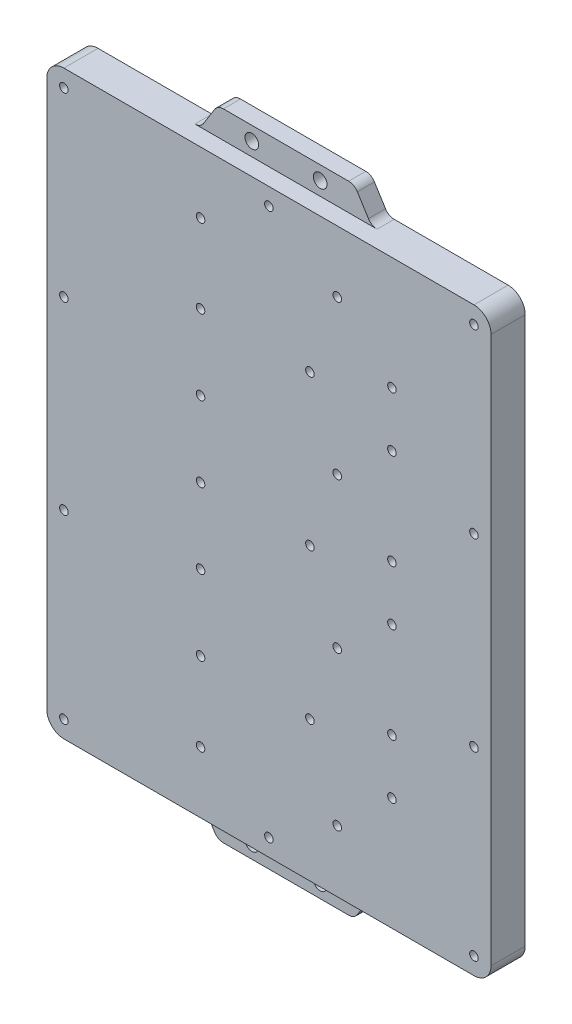
SolidWorks part; units mm, degrees
ref_plane "Front Plane" through (0, 0, 0) normal (0, 0, 1) x (1, 0, 0)
ref_plane "Top Plane" through (0, 0, 0) normal (0, 1, 0) x (1, 0, 0)
ref_plane "Right Plane" through (0, 0, 0) normal (1, 0, 0) x (0, 0, -1)
sketch "Sketch1" plane through (0, 0, 0) normal (0, 0, 1) x (1, 0, 0)
  line L0 (0, 0) -> (0, 173.9814) construction
  line L1 (-60, -85) -> (-26.6627, -85)
  line L2 (-65, -80) -> (-65, 80)
  line L3 (-60, 85) -> (-26.6627, 85)
  line L4 (65, -80) -> (65, 80)
  line L5 (-65, -85) -> (65, 85) construction
  line L6 (-65, 85) -> (65, -85) construction
  line L7 (18.3373, 93) -> (-18.3373, 93)
  line L8 (20.8813, 91.59) -> (24.1187, 86.41)
  line L9 (26.6627, 85) -> (60, 85)
  line L10 (-20.8813, 91.59) -> (-24.1187, 86.41)
  line L11 (0, 0) -> (119.7627, 0) construction
  line L12 (20.8813, -91.59) -> (24.1187, -86.41)
  line L13 (18.3373, -93) -> (-18.3373, -93)
  line L14 (-20.8813, -91.59) -> (-24.1187, -86.41)
  line L15 (26.6627, -85) -> (60, -85)
  arc A0 (-60, -85) -> (-65, -80) centre (-60, -80) cw
  arc A1 (60, -85) -> (65, -80) centre (60, -80) ccw
  arc A2 (60, 85) -> (65, 80) centre (60, 80) cw
  arc A3 (-65, 80) -> (-60, 85) centre (-60, 80) cw
  arc A4 (18.3373, 93) -> (20.8813, 91.59) centre (18.3373, 90) cw
  arc A5 (24.1187, 86.41) -> (26.6627, 85) centre (26.6627, 88) ccw
  arc A6 (-24.1187, 86.41) -> (-26.6627, 85) centre (-26.6627, 88) cw
  arc A7 (-18.3373, 93) -> (-20.8813, 91.59) centre (-18.3373, 90) ccw
  arc A8 (24.1187, -86.41) -> (26.6627, -85) centre (26.6627, -88) cw
  arc A9 (18.3373, -93) -> (20.8813, -91.59) centre (18.3373, -90) ccw
  arc A10 (-18.3373, -93) -> (-20.8813, -91.59) centre (-18.3373, -90) cw
  arc A11 (-24.1187, -86.41) -> (-26.6627, -85) centre (-26.6627, -88) ccw
  circle A12 centre (-10, 89) radius 2
  circle A13 centre (10, 89) radius 2
  circle A14 centre (10, -89) radius 2
  circle A15 centre (-10, -89) radius 2
  point P0 (0, 0)
  point P26 (20, 93)
  point P30 (25, 85)
  point P37 (0, 93)
  point P52 (-8.8094, 89.1796)
  point P53 (-7.2007, 90.1588)
  dimension "D3" = 5
  dimension "D7" = 3
  dimension "D8" = 3
  dimension "D11" = 4
  dimension "D1" = 130
  dimension "D2" = 170
  dimension "D4" = 8
  dimension "D5" = 20
  dimension "D6" = 25
  dimension "D9" = 10
  dimension "D10" = 4
extrude "Boss-Extrude1" add sketch "Sketch1" along normal blind 5
sketch "Sketch2" plane through (0, 0, 5) normal (0, 0, 1) x (1, 0, 0)
  line L1 (60, -85) -> (-60, -85)
  line L2 (65, -80) -> (65, 80)
  line L3 (60, 85) -> (-60, 85)
  line L4 (-65, -80) -> (-65, 80)
  line L5 (65, -85) -> (-65, 85) construction
  line L6 (65, 85) -> (-65, -85) construction
  arc A0 (-65, 80) -> (-60, 85) centre (-60, 80) cw
  arc A1 (60, 85) -> (65, 80) centre (60, 80) cw
  arc A2 (65, -80) -> (60, -85) centre (60, -80) cw
  arc A3 (-60, -85) -> (-65, -80) centre (-60, -80) cw
  arc A4 (-65, -80) -> (-60, -85) centre (-60, -80) ccw construction
  point P0 (0, 0)
extrude "Boss-Extrude2" add sketch "Sketch2" along normal blind 5
sketch "Sketch3" plane through (0, 0, 10) normal (0, 0, 1) x (1, 0, 0)
  line L0 (0, 0) -> (0, 112.7177) construction
  line L1 (0, 0) -> (126.367, 0) construction
  line L2 (-20, 106.3032) -> (-20, -110.6955) construction
  line L3 (36, 108.5453) -> (36, -108.1132) construction
  line L4 (-65, 80) -> (-65, -80) construction
  line L5 (-60, -85) -> (60, -85) construction
  line L7 (-20, -67) -> (21.9568, -67) construction
  line L8 (-20, -44) -> (26.4429, -44) construction
  circle A0 centre (60, -27) radius 1.25
  circle A1 centre (60, -80) radius 1.25
  circle A2 centre (-60, -27) radius 1.25
  circle A3 centre (-60, -80) radius 1.25
  circle A4 centre (0, -80) radius 1.25
  circle A5 centre (60, 27) radius 1.25
  circle A6 centre (60, 80) radius 1.25
  circle A7 centre (0, 80) radius 1.25
  circle A8 centre (-60, 27) radius 1.25
  circle A9 centre (-60, 80) radius 1.25
  circle A10 centre (-20, -67) radius 1.25
  circle A11 centre (-20, -44) radius 1.25
  circle A12 centre (-20, -22) radius 1.25
  circle A13 centre (-20, 0) radius 1.25
  circle A14 centre (-20, 22) radius 1.25
  circle A15 centre (-20, 44) radius 1.25
  circle A16 centre (-20, 67) radius 1.25
  circle A17 centre (36, -52) radius 1.25
  circle A18 centre (36, -36) radius 1.25
  circle A19 centre (36, 8) radius 1.25
  circle A20 centre (36, -8) radius 1.25
  circle A21 centre (36, 52) radius 1.25
  circle A22 centre (36, 36) radius 1.25
  circle A23 centre (20, -67) radius 1.25
  circle A24 centre (20, -22) radius 1.25
  circle A25 centre (20, 22) radius 1.25
  circle A26 centre (20, 67) radius 1.25
  circle A27 centre (12, -44) radius 1.25
  circle A28 centre (12, 0) radius 1.25
  circle A29 centre (12, 44) radius 1.25
  dimension "D2" = 2.5
  dimension "D3" = 2.5
  dimension "D4" = 2.5
  dimension "D7" = 2.5
  dimension "D8" = 2.5
  dimension "D13" = 2.5
  dimension "D15" = 2
  dimension "D16" = 2.5
  dimension "D20" = 2.5
  dimension "D1" = 27
  dimension "D5" = 45
  dimension "D6" = 101
  dimension "D9" = 18
  dimension "D10" = 23
  dimension "D14" = 33
  dimension "D17" = 40
  dimension "D21" = 32
  dimension "D11" = 5
  dimension "D12" = 2
  dimension "D18" = 2
  dimension "D19" = 2
extrude "Cut-Extrude1" cut sketch "Sketch3" against normal blind 5
cosmetic thread "Cosmetic Thread1"
cosmetic thread "Cosmetic Thread2"
cosmetic thread "Cosmetic Thread3"
cosmetic thread "Cosmetic Thread4"
cosmetic thread "Cosmetic Thread5"
cosmetic thread "Cosmetic Thread6"
cosmetic thread "Cosmetic Thread7"
cosmetic thread "Cosmetic Thread8"
cosmetic thread "Cosmetic Thread9"
cosmetic thread "Cosmetic Thread10"
cosmetic thread "Cosmetic Thread11"
cosmetic thread "Cosmetic Thread12"
cosmetic thread "Cosmetic Thread13"
cosmetic thread "Cosmetic Thread14"
cosmetic thread "Cosmetic Thread15"
cosmetic thread "Cosmetic Thread16"
cosmetic thread "Cosmetic Thread17"
cosmetic thread "Cosmetic Thread18"
cosmetic thread "Cosmetic Thread19"
cosmetic thread "Cosmetic Thread20"
cosmetic thread "Cosmetic Thread21"
cosmetic thread "Cosmetic Thread22"
cosmetic thread "Cosmetic Thread23"
cosmetic thread "Cosmetic Thread24"
cosmetic thread "Cosmetic Thread25"
cosmetic thread "Cosmetic Thread26"
cosmetic thread "Cosmetic Thread27"
cosmetic thread "Cosmetic Thread28"
cosmetic thread "Cosmetic Thread29"
cosmetic thread "Cosmetic Thread30"
cosmetic thread "Cosmetic Thread31"
cosmetic thread "Cosmetic Thread32"
cosmetic thread "Cosmetic Thread33"
cosmetic thread "Cosmetic Thread34"
cosmetic thread "Cosmetic Thread35"
cosmetic thread "Cosmetic Thread36"
cosmetic thread "Cosmetic Thread37"
cosmetic thread "Cosmetic Thread38"
cosmetic thread "Cosmetic Thread39"
cosmetic thread "Cosmetic Thread40"
cosmetic thread "Cosmetic Thread41"
cosmetic thread "Cosmetic Thread42"
cosmetic thread "Cosmetic Thread43"
cosmetic thread "Cosmetic Thread44"
cosmetic thread "Cosmetic Thread45"
cosmetic thread "Cosmetic Thread46"
cosmetic thread "Cosmetic Thread47"
cosmetic thread "Cosmetic Thread48"
cosmetic thread "Cosmetic Thread49"
cosmetic thread "Cosmetic Thread50"
cosmetic thread "Cosmetic Thread51"
cosmetic thread "Cosmetic Thread52"
cosmetic thread "Cosmetic Thread53"
cosmetic thread "Cosmetic Thread54"
cosmetic thread "Cosmetic Thread55"
cosmetic thread "Cosmetic Thread56"
cosmetic thread "Cosmetic Thread57"
cosmetic thread "Cosmetic Thread58"
cosmetic thread "Cosmetic Thread59"
cosmetic thread "Cosmetic Thread60"
